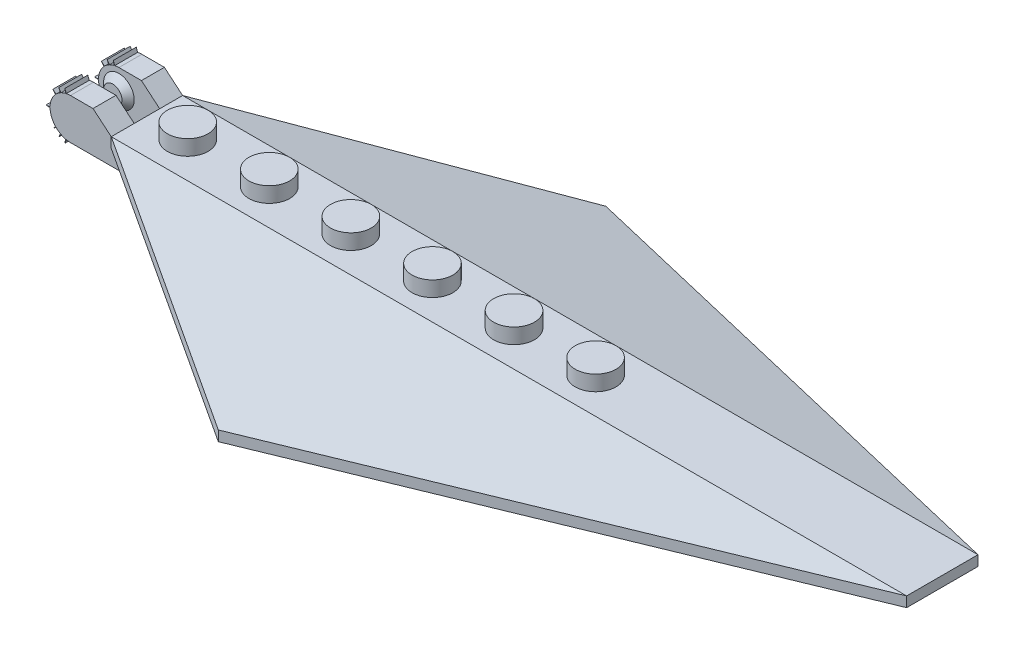
SolidWorks part; units mm, degrees
material "ABS"
ref_plane "Front Plane" through (0, 0, 0) normal (0, 0, 1) x (1, 0, 0)
ref_plane "Top Plane" through (0, 0, 0) normal (0, 1, 0) x (1, 0, 0)
ref_plane "Right Plane" through (0, 0, 0) normal (1, 0, 0) x (0, 0, -1)
sketch "Sketch1" plane through (0, 0, 0) normal (0, 0, 1) x (1, 0, 0)
  line L0 (-30.48, 0) -> (30.48, 0)
  line L1 (30.48, 0) -> (30.48, -3.175)
  line L2 (30.48, -3.175) -> (-30.48, -3.175)
  line L3 (-30.48, -3.175) -> (-30.48, 0)
  point P3 (0, 0)
  dimension "D1" = 3.175
  dimension "D2" = 60.96
extrude "Boss-Extrude1" add sketch "Sketch1" along normal mid plane 8.89
sketch "Sketch3" plane through (0, 0, 0) normal (0, 1, 0) x (1, 0, 0)
  line L0 (-30.48, 0) -> (-10.16, 0) construction
  line L3 (-30.48, -4.445) -> (-30.48, 4.445) construction
  line L7 (-30.48, 4.445) -> (-20.32, -4.445) construction
  line L8 (30.48, -4.445) -> (-30.48, -4.445) construction
  line L9 (-20.32, -4.445) -> (-10.16, 4.445) construction
  line L10 (30.48, 4.445) -> (-30.48, 4.445) construction
  line L11 (0, 0) -> (0, 8.0136) construction
  line L14 (-10.16, 4.445) -> (0, -4.445) construction
  circle A3 centre (-25.4, 0) radius 2.54
  circle A4 centre (-15.24, 0) radius 2.54
  circle A5 centre (-5.08, 0) radius 2.54
  circle A6 centre (5.08, 0) radius 2.54
  circle A7 centre (15.24, 0) radius 2.54
  circle A8 centre (25.4, 0) radius 2.54
  dimension "D1" = 5.08
extrude "Boss-Extrude2" add sketch "Sketch3" along normal blind 1.905
sketch "Sketch4" plane through (0, 0, 0) normal (0, 1, 0) x (1, 0, 0)
  line L0 (30.48, 4.445) -> (68.58, 4.445)
  line L1 (-30.48, -4.445) -> (-30.48, 4.445) construction
  line L2 (30.48, -4.445) -> (30.48, 4.445) construction
  line L3 (30.48, -4.445) -> (30.48, 4.445)
  line L4 (30.48, -4.445) -> (68.58, -4.445)
  line L5 (68.58, -4.445) -> (68.58, 4.445)
  dimension "D1" = 99.06
extrude "Boss-Extrude3" add sketch "Sketch4" against normal blind 1.27
sketch "Sketch5" plane through (0, 0, 0) normal (1, 0, 0) x (0, 0, -1)
  line L0 (4.445, 0) -> (24.13, -5.2746)
  line L1 (4.445, -1.27) -> (4.445, 0) construction
  line L2 (4.445, 0) -> (4.445, -1.27)
  line L3 (4.445, -1.27) -> (24.13, -6.5446)
  line L4 (24.13, -6.5446) -> (24.13, -5.2746)
  line L5 (0, 0) -> (0, -4.9356) construction
  line L6 (-24.13, -6.5446) -> (-24.13, -5.2746)
  line L7 (-4.445, -1.27) -> (-24.13, -6.5446)
  line L8 (-4.445, 0) -> (-4.445, -1.27)
  line L9 (-4.445, 0) -> (-24.13, -5.2746)
  dimension "D1" = 75
  dimension "D2" = 48.26
extrude "Boss-Extrude4" add sketch "Sketch5" along normal through all and the other way through all
sketch "Sketch7" plane through (0, 0, 0) normal (0, 1, 0) x (1, 0, 0)
  line L0 (-30.48, 4.445) -> (2.54, 24.13)
  line L1 (68.58, 24.13) -> (-30.48, 24.13) construction
  line L2 (2.54, 24.13) -> (68.58, 4.445)
  line L3 (-30.48, 0) -> (-42.2019, 0) construction
  line L4 (-30.48, -4.445) -> (-30.48, 4.445) construction
  line L5 (-30.48, -4.445) -> (2.54, -24.13)
  line L6 (2.54, -24.13) -> (68.58, -4.445)
  line L7 (-30.48, 4.445) -> (-30.48, 24.13)
  line L8 (-30.48, 24.13) -> (68.58, 24.13)
  line L9 (68.58, 24.13) -> (68.58, 4.445)
  line L10 (-30.48, -4.445) -> (-30.48, -24.13)
  line L11 (-30.48, -24.13) -> (2.54, -24.13)
  line L12 (68.58, -24.13) -> (68.58, -4.445)
  line L13 (2.54, -24.13) -> (68.58, -24.13)
  dimension "D1" = 33.02
extrude "Cut-Extrude1" cut sketch "Sketch7" against normal through all both and the other way through all contours L8 L7 L0 | L9 L8 L2 | L6 L13 L12 | L10 L11 L5
sketch "Sketch8" plane through (0, 0, 0) normal (0, 0, 1) x (1, 0, 0)
  line L0 (-30.48, -3.175) -> (-35.56, -3.175)
  line L1 (68.58, 0) -> (-30.48, 0) construction
  line L2 (-30.48, 0) -> (-32.7503, 1.905)
  line L3 (-32.7503, 1.905) -> (-35.56, 1.905)
  line L4 (-35.56, -3.175) -> (-35.56, 1.905) construction
  line L5 (-38.0996, -0.6793) -> (-38.6057, -0.635)
  line L6 (-38.6057, -0.635) -> (-38.0996, -0.5907)
  line L7 (-30.48, 0) -> (-30.48, -3.175)
  line L9 (-37.4192, -2.3656) -> (-37.7466, -2.7559)
  line L10 (-37.7466, -2.7559) -> (-37.3576, -2.4295)
  line L11 (-37.7466, 1.4859) -> (-37.3576, 1.1595)
  line L12 (-37.4192, 1.0956) -> (-37.7466, 1.4859)
  line L13 (-36.8069, -2.8479) -> (-37.0205, -3.3061)
  line L14 (-36.1685, -3.101) -> (-36.2561, -3.5981)
  line L15 (-36.2561, -3.5981) -> (-36.0824, -3.1207)
  line L16 (-36.1685, 1.831) -> (-36.2561, 2.3281)
  line L17 (-36.2561, 2.3281) -> (-36.0824, 1.8507)
  line L18 (-37.0205, -3.3061) -> (-36.7291, -2.8899)
  line L19 (-37.0205, 2.0361) -> (-36.7291, 1.6199)
  line L20 (-36.8069, 1.5779) -> (-37.0205, 2.0361)
  arc A0 (-35.56, 1.905) -> (-36.0824, 1.8507) centre (-35.56, -0.635) ccw
  arc A1 (-36.1685, 1.831) -> (-36.7291, 1.6199) centre (-35.56, -0.635) ccw
  arc A2 (-36.8069, 1.5779) -> (-37.3576, 1.1595) centre (-35.56, -0.635) ccw
  arc A3 (-37.4192, 1.0956) -> (-38.0996, -0.5907) centre (-35.56, -0.635) ccw
  arc A4 (-38.0996, -0.6793) -> (-37.4192, -2.3656) centre (-35.56, -0.635) ccw
  arc A5 (-37.3576, -2.4295) -> (-36.8069, -2.8479) centre (-35.56, -0.635) ccw
  arc A6 (-36.7291, -2.8899) -> (-36.1685, -3.101) centre (-35.56, -0.635) ccw
  arc A7 (-36.0824, -3.1207) -> (-35.56, -3.175) centre (-35.56, -0.635) ccw
  dimension "D1" = 5.08
  dimension "D2" = 5.08
  dimension "D3" = 140
  dimension "D4" = 5.08
  dimension "D5" = 0.508
  dimension "D9" = 0.508
  dimension "D13" = 0.508
extrude "Boss-Extrude5" add sketch "Sketch8" along normal up to surface and the other way up to surface up to face at (0, -2.2225, 4.445) other way up to face at (0, -2.2225, -4.445)
sketch "Sketch9" plane through (0, 0, 0) normal (0, 1, 0) x (1, 0, 0)
  line L0 (-30.48, -4.445) -> (-30.48, 4.445) construction
  line L1 (-42.1918, 1.5875) -> (-30.48, 1.5875)
  line L2 (-42.1918, 1.5875) -> (-42.1918, -1.5875)
  line L3 (-42.1918, -1.5875) -> (-30.48, -1.5875)
  line L4 (-30.48, 1.5875) -> (-30.48, -1.5875)
  point P8 (-42.1918, 0)
  dimension "D1" = 3.175
extrude "Cut-Extrude2" cut sketch "Sketch9" against normal through all both and the other way through all
sketch "Sketch10" plane through (0, 0, -1.5875) normal (0, 0, 1) x (1, 0, 0)
  circle A0 centre (-35.56, -0.635) radius 1.905
  dimension "D1" = 3.81
extrude "Boss-Extrude6" add sketch "Sketch10" along normal blind 0.762 draft 45
mirror "Mirror1" about plane through (0, 0, 0) normal (0, 0, 1) of "Boss-Extrude6"
sketch "Sketch11" plane through (0, -3.175, 0) normal (0, -1, 0) x (1, 0, 0)
  line L4 (-29.21, 2.54) -> (-29.21, -2.54)
  line L5 (-29.21, -2.54) -> (29.21, -2.54)
  line L6 (-29.21, 2.54) -> (29.21, 2.54)
  line L7 (29.21, 2.54) -> (29.21, -2.54)
extrude "Cut-Extrude3" cut sketch "Sketch11" against normal blind 1.905
sketch "Sketch12" plane through (0, -1.27, 0) normal (0, -1, 0) x (1, 0, 0)
  circle A0 centre (-25.4, 0) radius 1.905
  circle A1 centre (-15.24, 0) radius 1.905
  circle A2 centre (-5.08, 0) radius 1.905
  circle A3 centre (5.08, 0) radius 1.905
  circle A4 centre (15.24, 0) radius 1.905
  circle A5 centre (25.4, 0) radius 1.905
  dimension "D1" = 3.81
extrude "Cut-Extrude5" cut sketch "Sketch12" against normal blind 2.54
sketch "Sketch13" plane through (0, -1.27, 0) normal (0, -1, 0) x (1, 0, 0)
  line L0 (-23.495, 0) -> (-17.145, 0) construction
  line L1 (-13.335, 0) -> (-6.985, 0) construction
  line L2 (0, -2.2915) -> (0, 0) construction
  line L3 (-5.08, 1.905) -> (-5.08, -5.6224) construction
  circle A0 centre (-25.4, 0) radius 1.905 construction
  circle A1 centre (-15.24, 0) radius 1.905 construction
  circle A2 centre (-5.08, 0) radius 1.905 construction
  circle A3 centre (-20.32, 0) radius 1.905
  circle A4 centre (-10.16, 0) radius 1.905
  circle A5 centre (-20.32, 0) radius 0.9525
  circle A6 centre (-10.16, 0) radius 0.9525
  circle A7 centre (10.16, 0) radius 0.9525
  circle A8 centre (20.32, 0) radius 0.9525
  circle A9 centre (10.16, 0) radius 1.905
  circle A10 centre (20.32, 0) radius 1.905
  circle A11 centre (0, 0) radius 0.9525
  circle A12 centre (0, 0) radius 1.905
  dimension "D1" = 3.81
  dimension "D2" = 1.905
  dimension "D3" = 1.905
extrude "Boss-Extrude7" add sketch "Sketch13" along normal up to surface (1.905 mm away) up to face at (0, -3.175, 0)
